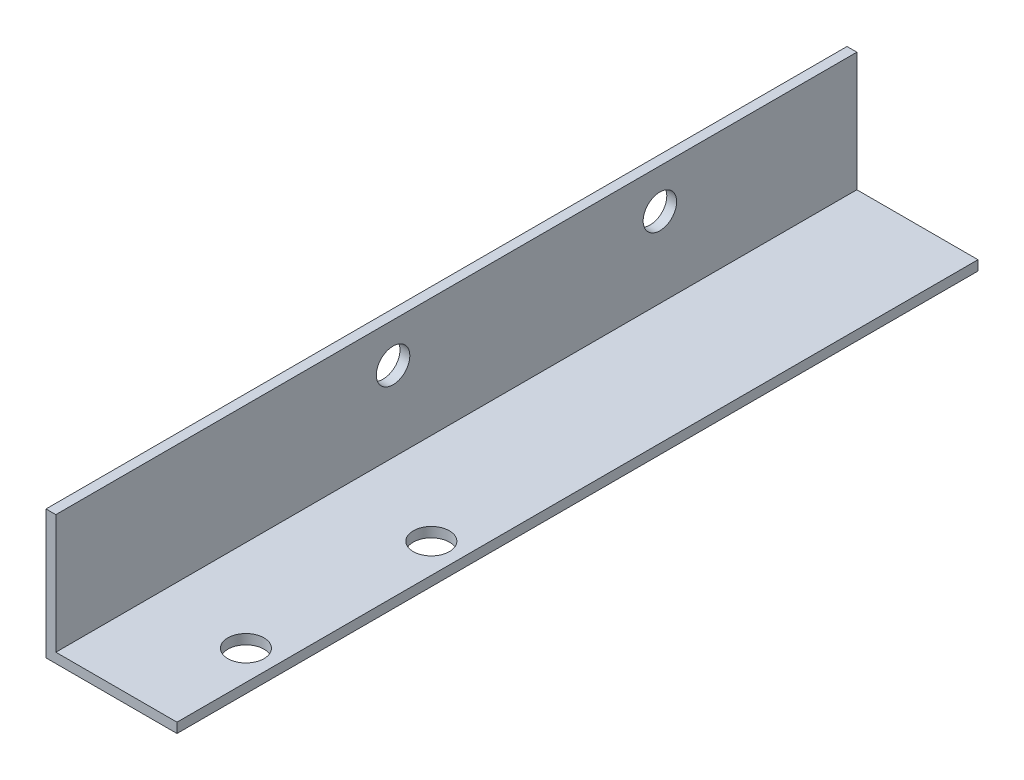
SolidWorks part; units mm, degrees
material "6063-T5"
ref_plane "Front Plane" through (0, 0, 0) normal (0, 0, 1) x (1, 0, 0)
ref_plane "Top Plane" through (0, 0, 0) normal (0, 1, 0) x (1, 0, 0)
ref_plane "Right Plane" through (0, 0, 0) normal (1, 0, 0) x (0, 0, -1)
sketch "Sketch1" plane through (0, 0, 0) normal (0, 0, 1) x (1, 0, 0)
  line L0 (0, 18.15) -> (0, 0)
  line L1 (0, 0) -> (18.45, 0)
  line L2 (-1.5, 18.15) -> (-1.5, -1.5)
  line L3 (-1.5, -1.5) -> (18.45, -1.5)
  line L4 (-1.5, 18.15) -> (0, 18.15)
  line L5 (18.45, 0) -> (18.45, -1.5)
  dimension "D2" = 19.65
  dimension "D3" = 19.95
  dimension "D1" = 1.5
extrude "Boss-Extrude1" add sketch "Sketch1" along normal blind 122
sketch "Sketch2" plane through (0, -1.5, 0) normal (0, -1, 0) x (-1, 0, 0)
  line L0 (-18.45, -122) -> (-18.45, 0) construction
  line L1 (1.5, -122) -> (-18.45, -122) construction
  circle A0 centre (-13.95, -107) radius 2.75
  circle A1 centre (-13.95, -78.76) radius 2.75
  dimension "D1" = 5.5
  dimension "D2" = 28.24
  dimension "D3" = 4.5
  dimension "D4" = 15
  dimension "D5" = 4.5
extrude "Cut-Extrude1" cut sketch "Sketch2" against normal through all
sketch "Sketch3" plane through (-1.5, 0, 0) normal (-1, 0, 0) x (0, 0, 1)
  line L0 (122, -1.5) -> (0, -1.5) construction
  line L1 (0, 18.15) -> (0, -1.5) construction
  circle A0 centre (30, 12.15) radius 2.55
  circle A1 centre (70.64, 12.15) radius 2.55
  dimension "D1" = 5.1
  dimension "D2" = 40.64
  dimension "D4" = 30
  dimension "D5" = 13.65
  dimension "D3" = 13.65
extrude "Cut-Extrude2" cut sketch "Sketch3" against normal through all
